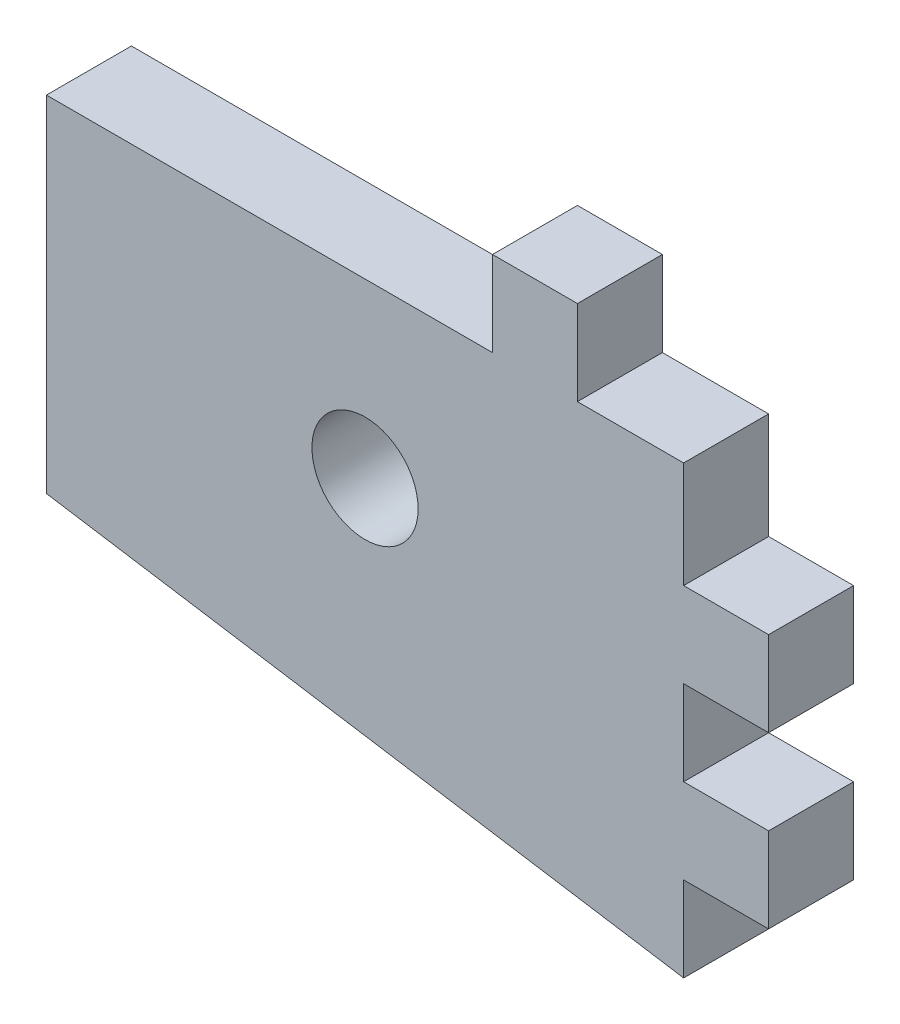
SolidWorks part; units mm, degrees
material "Cedar"
ref_plane "Front Plane" through (0, 0, 0) normal (0, 0, 1) x (1, 0, 0)
ref_plane "Top Plane" through (0, 0, 0) normal (0, 1, 0) x (1, 0, 0)
ref_plane "Right Plane" through (0, 0, 0) normal (1, 0, 0) x (0, 0, -1)
sketch "Sketch1" plane through (0, 0, 0) normal (0, 0, 1) x (1, 0, 0)
  line L0 (0, 9.5395) -> (0, -11.4605)
  line L1 (-30, 9.5395) -> (-30, -6.709)
  line L2 (-30, 9.5395) -> (0, 9.5395)
  line L3 (-30, -6.709) -> (0, -11.4605)
  line L4 (-30, -6.709) -> (0, -6.709) construction
  line L5 (0, -6.709) -> (-30, 9.5395) construction
  line L6 (0, 9.5395) -> (-30, -6.709) construction
  circle A0 centre (-15, 1.4152) radius 2.5
  point P7 (-15, 1.4152)
  dimension "D6" = 5
  dimension "D1" = 21
  dimension "D2" = 81
  dimension "D3" = 30
extrude "Boss-Extrude1" add sketch "Sketch1" along normal blind 4
sketch "Sketch2" plane through (0, 0, 4) normal (0, 0, 1) x (1, 0, 0)
  line L1 (0, -11.4605) -> (0, 9.5395) construction
  line L2 (0, 0.5395) -> (4, 0.5395)
  line L3 (0, 0.5395) -> (0, 4.5395)
  line L4 (0, 4.5395) -> (4, 4.5395)
  line L5 (0, 9.5395) -> (-30, 9.5395) construction
  line L6 (-5, 9.5395) -> (-9, 9.5395)
  line L7 (-5, 9.5395) -> (-5, 13.5395)
  line L8 (-5, 13.5395) -> (-9, 13.5395)
  line L9 (-9, 9.5395) -> (-9, 13.5395)
  line L10 (4, 0.5395) -> (4, 4.5395)
  line L12 (0, -3.4605) -> (4, -3.4605)
  line L13 (0, -3.4605) -> (0, -7.4605)
  line L14 (0, -7.4605) -> (4, -7.4605)
  line L15 (4, -3.4605) -> (4, -7.4605)
  dimension "D1" = 5
  dimension "D2" = 4
  dimension "D3" = 4
  dimension "D4" = 4
  dimension "D5" = 5
  dimension "D6" = 4
  dimension "D7" = 4
extrude "Boss-Extrude2" add sketch "Sketch2" against normal blind 4
